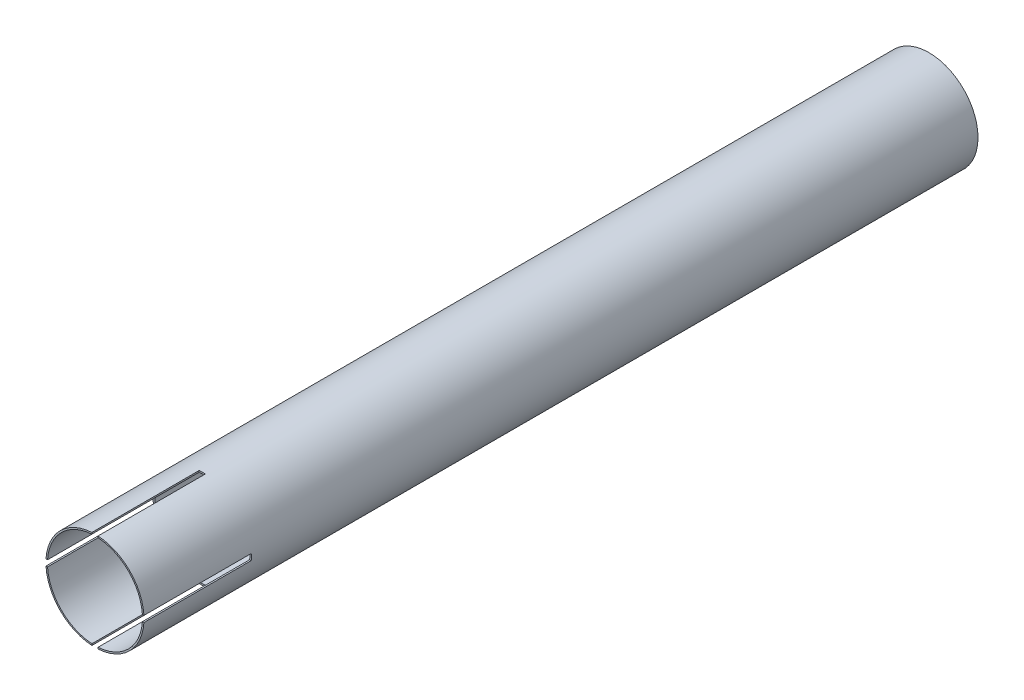
SolidWorks part; units mm, degrees
ref_plane "Front Plane" through (0, 0, 0) normal (0, 0, 1) x (1, 0, 0)
ref_plane "Top Plane" through (0, 0, 0) normal (0, 1, 0) x (1, 0, 0)
ref_plane "Right Plane" through (0, 0, 0) normal (1, 0, 0) x (0, 0, -1)
sketch "Sketch1" plane through (0, 0, 0) normal (0, 0, 1) x (1, 0, 0)
  circle A0 centre (0, 0) radius 50.8
  circle A1 centre (0, 0) radius 49.2125
  dimension "D1" = 101.6
  dimension "D2" = 1.5875
extrude "Boss-Extrude1" add sketch "Sketch1" along normal blind 863.6
sketch "Sketch2" plane through (0, 0, 0) normal (0, 1, 0) x (1, 0, 0)
  line L0 (-50.8, -863.6) -> (50.8, -863.6) construction
  line L1 (3.175, -863.6) -> (-3.175, -863.6)
  line L2 (3.175, -863.6) -> (3.175, -752.475)
  line L3 (3.175, -752.475) -> (-3.175, -752.475)
  line L4 (-3.175, -863.6) -> (-3.175, -752.475)
  line L5 (0, -863.6) -> (0, -641.35) construction
  line L6 (-50.8, -863.6) -> (50.8, -863.6) construction
  point P12 (0, -863.6)
  point P13 (0, -752.475)
  dimension "D1" = 6.35
  dimension "D2" = 111.125
extrude "Cut-Extrude1" cut sketch "Sketch2" against normal through all and the other way through all
sketch "Sketch3" plane through (0, 0, 0) normal (1, 0, 0) x (0, 0, -1)
  line L0 (-863.6, 50.7007) -> (-863.6, -50.7007) construction
  line L1 (-863.6, 0) -> (-641.35, 0) construction
  line L2 (-863.6, 3.175) -> (-752.475, 3.175)
  line L3 (-863.6, 3.175) -> (-863.6, -3.175)
  line L4 (-863.6, -3.175) -> (-752.475, -3.175)
  line L5 (-752.475, 3.175) -> (-752.475, -3.175)
  point P11 (-752.475, 0)
  dimension "D1" = 111.125
  dimension "D2" = 6.35
extrude "Cut-Extrude2" cut sketch "Sketch3" against normal through all and the other way through all
